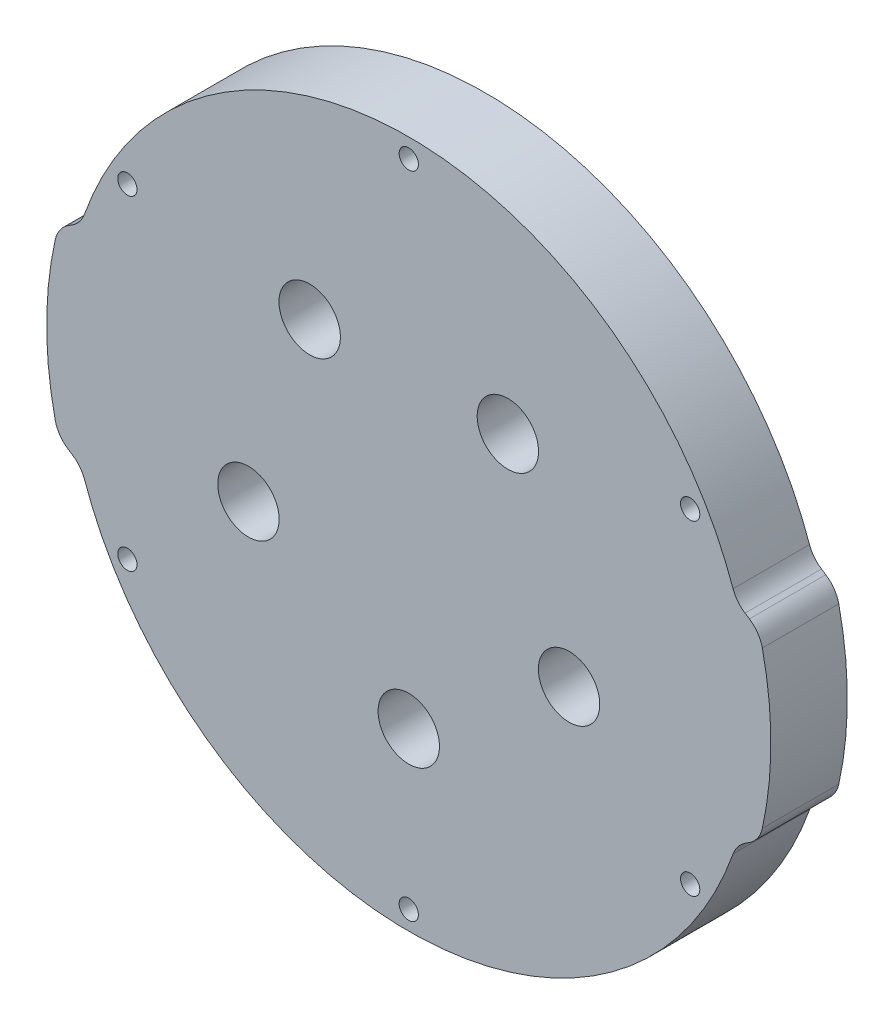
SolidWorks part; units mm, degrees
material "Acrylic (Medium-high impact)"
ref_plane "Front Plane" through (0, 0, 0) normal (0, 0, 1) x (1, 0, 0)
ref_plane "Top Plane" through (0, 0, 0) normal (0, 1, 0) x (1, 0, 0)
ref_plane "Right Plane" through (0, 0, 0) normal (1, 0, 0) x (0, 0, -1)
sketch "Sketch1" plane through (0, 0, 0) normal (0, 0, 1) x (1, 0, 0)
  line L0 (54.4047, 17.5) -> (58.2497, 15)
  line L1 (54.4047, -17.5) -> (58.2497, -15)
  line L2 (-54.4047, 17.5) -> (-58.2497, 15)
  line L3 (-54.4047, -17.5) -> (-58.2497, -15)
  line L4 (0, 53.975) -> (0, 0) construction
  line L5 (0, 0) -> (-46.7437, 26.9875) construction
  line L6 (-46.7437, 26.9875) -> (-49.4934, 28.575) construction
  arc A0 (54.4047, 17.5) -> (-54.4047, 17.5) centre (0, 0) ccw
  circle A1 centre (0, 53.975) radius 1.6
  circle A2 centre (46.7437, 26.9875) radius 1.6
  circle A3 centre (46.7437, -26.9875) radius 1.6
  circle A4 centre (0, -53.975) radius 1.6
  circle A5 centre (-46.7437, -26.9875) radius 1.6
  circle A6 centre (-46.7437, 26.9875) radius 1.6
  arc A7 (58.2497, -15) -> (58.2497, 15) centre (0, 0) ccw
  arc A8 (-58.2497, 15) -> (-58.2497, -15) centre (0, 0) ccw
  arc A9 (-54.4047, -17.5) -> (54.4047, -17.5) centre (0, 0) ccw
  point P17 (0, 0)
  point P26 (-60.15, 0)
  point P27 (60.15, 0)
  dimension "D1" = 114.3
  dimension "D2" = 3.175
  dimension "D3" = 3.2
  dimension "D7" = 3
  dimension "D5" = 35
  dimension "D6" = 30
  dimension "D8" = 60
  dimension "D9" = 3.175
  dimension "D4" = 6
extrude "Boss-Extrude1" add sketch "Sketch1" along normal blind 12.7
sketch "Sketch6" plane through (0, 0, 0) normal (0, 0, -1) x (-1, 0, 0)
  line L0 (-26.6296, -8.6525) -> (0, 0) construction
  line L1 (0, 0) -> (0, -28) construction
  line L2 (26.6296, -8.6525) -> (0, 0) construction
  line L3 (0, 0) -> (16.458, 22.6525) construction
  line L4 (-16.458, 22.6525) -> (0, 0) construction
  line L5 (0, -28) -> (-26.6296, -8.6525) construction
  line L6 (-26.6296, -8.6525) -> (-16.458, 22.6525) construction
  line L7 (-16.458, 22.6525) -> (16.458, 22.6525) construction
  line L8 (16.458, 22.6525) -> (26.6296, -8.6525) construction
  line L9 (26.6296, -8.6525) -> (0, -28) construction
  circle A0 centre (16.458, 22.6525) radius 5.1
  circle A1 centre (-26.6296, -8.6525) radius 5.1
  circle A4 centre (26.6296, -8.6525) radius 5.1
  circle A5 centre (-16.458, 22.6525) radius 5.1
  circle A8 centre (0, -28) radius 5.1
  circle A9 centre (0, 0) radius 44.45 construction
  circle A10 centre (-16.458, 22.6525) radius 9 construction
  circle A11 centre (26.6296, -8.6525) radius 9 construction
  circle A13 centre (16.458, 22.6525) radius 9 construction
  circle A14 centre (-26.6296, -8.6525) radius 9 construction
  circle A16 centre (0, -28) radius 9 construction
  dimension "D1" = 10.2
  dimension "D2" = 88.9
  dimension "D3" = 28
  dimension "D4" = 18
extrude "Cut-Extrude2" cut sketch "Sketch6" against normal through all
fillet "Fillet1" radius 5 8 edges at (58.2497, -15, 6.35) (54.4047, -17.5, 6.35) (58.2497, 15, 6.35) (54.4047, 17.5, 6.35) (-54.4047, -17.5, 6.35) (-58.2497, -15, 6.35) (-58.2497, 15, 6.35) (-54.4047, 17.5, 6.35)
sketch "Sketch7" plane through (0, 0, 12.7) normal (0, 0, 1) x (1, 0, 0)
  circle A0 centre (0, 0) radius 57.15
  circle A1 centre (0, 0) radius 44.45
  arc A2 (53.8721, 19.0768) -> (-53.8721, 19.0768) centre (0, 0) ccw construction
  dimension "D1" = 88.9
extrude "ANALYSIS-SUPPORT" [suppressed] add sketch "Sketch7" along normal blind 1
sketch "Sketch8" plane through (0, 0, 0) normal (0, 0, -1) x (-1, 0, 0)
  circle A0 centre (0, 53.975) radius 2.75
  circle A1 centre (-46.7437, 26.9875) radius 2.75
  circle A2 centre (-46.7437, -26.9875) radius 2.75
  circle A3 centre (0, -53.975) radius 2.75
  circle A4 centre (46.7437, -26.9875) radius 2.75
  circle A5 centre (46.7437, 26.9875) radius 2.75
  dimension "D1" = 5.5
extrude "ANALYSIS-SCREW-HEAD" [suppressed] add sketch "Sketch8" along normal blind 1
